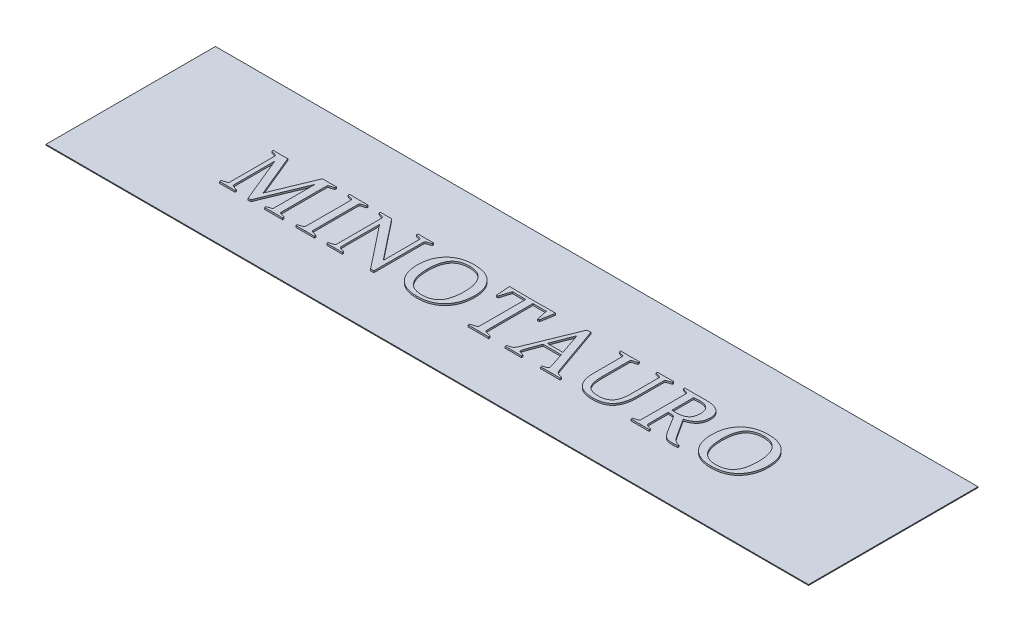
SolidWorks part; units mm, degrees
ref_plane "Front Plane" through (0, 0, 0) normal (0, 0, 1) x (1, 0, 0)
ref_plane "Top Plane" through (0, 0, 0) normal (0, 1, 0) x (1, 0, 0)
ref_plane "Right Plane" through (0, 0, 0) normal (1, 0, 0) x (0, 0, -1)
sketch "Sketch1" plane through (0, 0, 0) normal (0, 1, 0) x (1, 0, 0)
  line L1 (-90, 20) -> (90, 20)
  line L2 (-90, 20) -> (-90, -20)
  line L3 (-90, -20) -> (90, -20)
  line L4 (90, 20) -> (90, -20)
  line L5 (-90, 20) -> (90, -20) construction
  line L6 (-90, -20) -> (90, 20) construction
  point P0 (0, 0)
  dimension "D1" = 40
  dimension "D2" = 180
extrude "Boss-Extrude1" add sketch "Sketch1" along normal blind 0.2
sketch "Sketch2" plane through (0, 0.2, 0) normal (0, 1, 0) x (1, 0, 0)
  line L0 (-75, -7.3478) -> (75, -7.3478) construction
  text T0 "MINOTAURO" font "Constantia" height in points 48
  point P2 (0, 0)
  point P7 (0, 0)
  point P8 (0, 0)
  point P9 (0, 0)
extrude "Boss-Extrude2" add sketch "Sketch2" along normal blind 0.4
